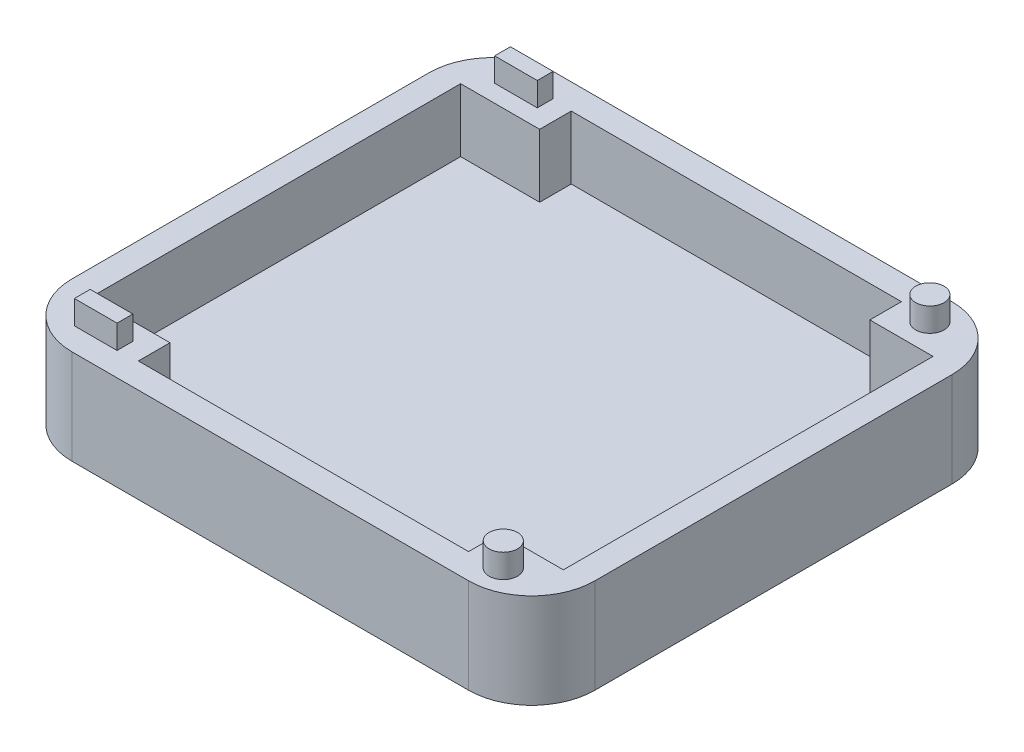
SolidWorks part; units mm, degrees
ref_plane "Front Plane" through (0, 0, 0) normal (0, 0, 1) x (1, 0, 0)
ref_plane "Top Plane" through (0, 0, 0) normal (0, 1, 0) x (1, 0, 0)
ref_plane "Right Plane" through (0, 0, 0) normal (1, 0, 0) x (0, 0, -1)
sketch "Sketch1" plane through (0, 0, 0) normal (0, 1, 0) x (1, 0, 0)
  line L1 (-42.037, -38.862) -> (42.037, -38.862)
  line L2 (-42.037, -38.862) -> (-42.037, 38.862)
  line L3 (-42.037, 38.862) -> (42.037, 38.862)
  line L4 (42.037, -38.862) -> (42.037, 38.862)
  line L5 (-42.037, -38.862) -> (42.037, 38.862) construction
  line L6 (-42.037, 38.862) -> (42.037, -38.862) construction
  point P0 (0, 0)
extrude "Boss-Extrude1" add sketch "Sketch1" along normal blind 5.08
sketch "Sketch2" plane through (0, 5.08, 0) normal (0, 1, 0) x (1, 0, 0)
  line L0 (42.037, -38.862) -> (42.037, 38.862) construction
  line L1 (-42.037, 38.862) -> (42.037, 38.862)
  line L2 (-42.037, 38.862) -> (-42.037, 34.798)
  line L3 (-42.037, 34.798) -> (42.037, 34.798)
  line L4 (42.037, 38.862) -> (42.037, 34.798)
  line L6 (-42.037, -38.862) -> (42.037, -38.862)
  line L7 (-42.037, -38.862) -> (-42.037, -34.798)
  line L8 (-42.037, -34.798) -> (42.037, -34.798)
  line L9 (42.037, -38.862) -> (42.037, -34.798)
  line L10 (-42.037, 34.798) -> (-37.973, 34.798)
  line L11 (-42.037, 34.798) -> (-42.037, -34.798)
  line L12 (-42.037, -34.798) -> (-37.973, -34.798)
  line L13 (-37.973, 34.798) -> (-37.973, -34.798)
  line L14 (42.037, 34.798) -> (37.973, 34.798)
  line L15 (42.037, 34.798) -> (42.037, -34.798)
  line L16 (42.037, -34.798) -> (37.973, -34.798)
  line L17 (37.973, 34.798) -> (37.973, -34.798)
  line L18 (-37.973, 34.798) -> (-25.273, 34.798)
  line L19 (-37.973, 34.798) -> (-37.973, 29.718)
  line L20 (-37.973, 29.718) -> (-25.273, 29.718)
  line L21 (-25.273, 34.798) -> (-25.273, 29.718)
  line L22 (37.973, 34.798) -> (27.813, 34.798)
  line L23 (37.973, 34.798) -> (37.973, 29.718)
  line L24 (37.973, 29.718) -> (27.813, 29.718)
  line L25 (27.813, 34.798) -> (27.813, 29.718)
  line L26 (-37.973, -34.798) -> (-25.273, -34.798)
  line L27 (-37.973, -34.798) -> (-37.973, -29.718)
  line L28 (-37.973, -29.718) -> (-25.273, -29.718)
  line L29 (-25.273, -34.798) -> (-25.273, -29.718)
  line L30 (37.973, -34.798) -> (27.813, -34.798)
  line L31 (37.973, -34.798) -> (37.973, -29.718)
  line L32 (37.973, -29.718) -> (27.813, -29.718)
  line L33 (27.813, -34.798) -> (27.813, -29.718)
  dimension "D2" = 4.064
  dimension "D3" = 12.7
  dimension "D4" = 5.08
  dimension "D5" = 10.16
  dimension "D6" = 5.08
  dimension "D7" = 5.08
  dimension "D8" = 12.7
  dimension "D9" = 10.16
  dimension "D10" = 5.08
  dimension "D11" = 4.064
  dimension "D12" = 4.064
  dimension "D13" = 4.064
extrude "Boss-Extrude2" add sketch "Sketch2" along normal blind 10.16 contours L21 L3 L15 L17 | L21 L3 L13 L20 | L13 L3 L21 L8 | L8 L29 L28 L13 | L8 L21 L20 L15 | L33 L8 L17 L32 | L3 L17 L8 L15 | L3 L25 L24 L17
fillet "Fillet1" radius 10.16 4 edges at (-42.037, 7.62, -38.862) (42.037, 7.62, -38.862) (42.037, 7.62, 38.862) (-42.037, 7.62, 38.862)
sketch "Sketch3" plane through (0, 15.24, 0) normal (0, 1, 0) x (1, 0, 0)
  line L0 (-42.037, 28.702) -> (-42.037, -28.702) construction
  line L1 (31.877, 38.862) -> (-31.877, 38.862) construction
  line L2 (42.037, -28.702) -> (42.037, 28.702) construction
  line L3 (-35.306, 32.512) -> (-28.448, 32.512)
  line L4 (-35.306, 32.512) -> (-35.306, 35.052)
  line L5 (-35.306, 35.052) -> (-28.448, 35.052)
  line L6 (-28.448, 32.512) -> (-28.448, 35.052)
  line L7 (-35.306, 32.512) -> (-28.448, 35.052) construction
  line L8 (-35.306, 35.052) -> (-28.448, 32.512) construction
  circle A0 centre (32.893, 34.29) radius 2.286
  point P0 (-31.877, 33.782)
  point P5 (-31.877, 33.782)
  dimension "D3" = 9.144
  dimension "D1" = 10.16
  dimension "D2" = 5.08
  dimension "D4" = 4.572
extrude "Boss-Extrude3" add sketch "Sketch3" along normal blind 3.81
mirror "Mirror1" about plane through (0, 0, 0) normal (0, 0, 1) of "Boss-Extrude3"
